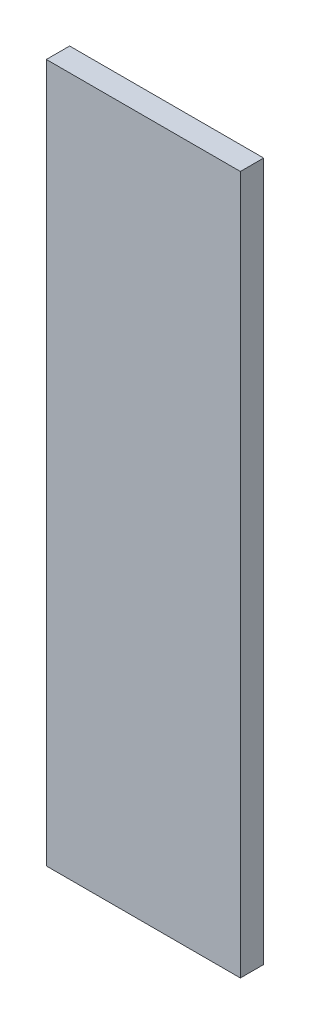
SolidWorks part; units mm, degrees
ref_plane "Alzado" through (0, 0, 0) normal (0, 0, 1) x (1, 0, 0)
ref_plane "Planta" through (0, 0, 0) normal (0, 1, 0) x (1, 0, 0)
ref_plane "Vista lateral" through (0, 0, 0) normal (1, 0, 0) x (0, 0, -1)
sketch "Croquis1" plane through (0, 0, 0) normal (0, 0, 1) x (1, 0, 0)
  line L1 (25, -90) -> (-25, -90)
  line L2 (25, -90) -> (25, 90)
  line L3 (25, 90) -> (-25, 90)
  line L4 (-25, -90) -> (-25, 90)
  line L5 (25, -90) -> (-25, 90) construction
  line L6 (25, 90) -> (-25, -90) construction
  point P0 (0, 0)
  dimension "D1" = 180
  dimension "D2" = 50
extrude "Saliente-Extruir1" add sketch "Croquis1" along normal blind 6
